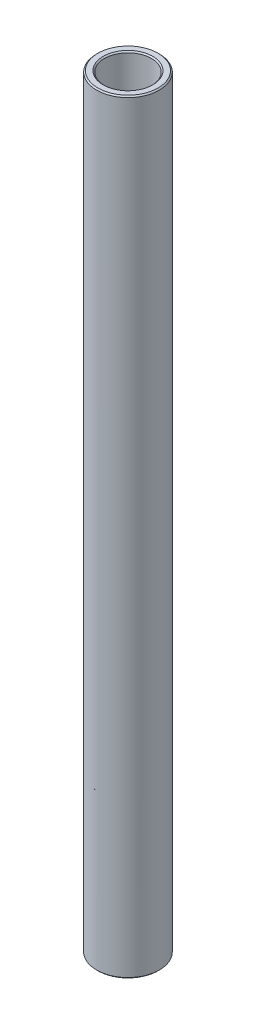
SolidWorks part; units mm, degrees
ref_plane "Front Plane" through (0, 0, 0) normal (0, 0, 1) x (1, 0, 0)
ref_plane "Top Plane" through (0, 0, 0) normal (0, 1, 0) x (1, 0, 0)
ref_plane "Right Plane" through (0, 0, 0) normal (1, 0, 0) x (0, 0, -1)
sketch "Sketch1" plane through (0, 0, 0) normal (0, 0, 1) x (1, 0, 0)
  line L0 (0, 11.6086) -> (0, -11.6086) construction
  line L1 (4.7625, 77.3906) -> (6.35, 77.3906)
  line L2 (6.35, 77.3906) -> (6.35, -77.3906)
  line L3 (6.35, -77.3906) -> (4.7625, -77.3906)
  line L4 (4.7625, -77.3906) -> (4.7625, 77.3906)
  line L5 (4.7625, 0) -> (0, 0) construction
  dimension "D1" = 9.525
  dimension "D2" = 12.7
  dimension "D3" = 154.7812
revolve "Revolve1" add sketch "Sketch1" angle 360 about L0
chamfer "Chamfer1" distance 0.254 angle 45 4 edges at (-4.7625, -77.3906, 0) (-6.35, -77.3906, 0) (-6.35, 77.3906, 0) (-4.7625, 77.3906, 0)
